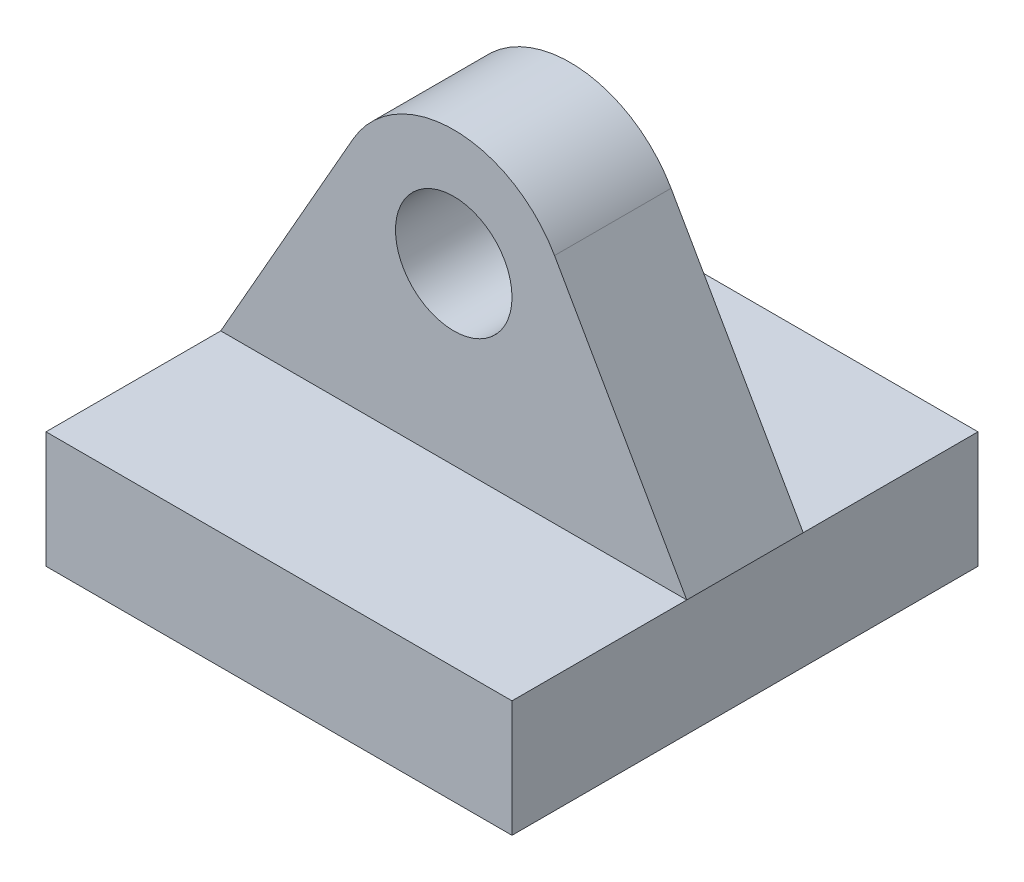
SolidWorks part; units mm, degrees
ref_plane "Front Plane" through (0, 0, 0) normal (0, 0, 1) x (1, 0, 0)
ref_plane "Top Plane" through (0, 0, 0) normal (0, 1, 0) x (1, 0, 0)
ref_plane "Right Plane" through (0, 0, 0) normal (1, 0, 0) x (0, 0, -1)
sketch "Sketch1" plane through (0, 0, 0) normal (0, 0, 1) x (1, 0, 0)
  line L1 (-12.7, -3.175) -> (12.7, -3.175)
  line L2 (-12.7, -3.175) -> (-12.7, 3.175)
  line L3 (-12.7, 3.175) -> (12.7, 3.175)
  line L4 (12.7, -3.175) -> (12.7, 3.175)
  line L5 (-12.7, -3.175) -> (12.7, 3.175) construction
  line L6 (-12.7, 3.175) -> (12.7, -3.175) construction
  point P0 (0, 0)
  dimension "D1" = 25.4
  dimension "D2" = 6.35
extrude "Boss-Extrude1" add sketch "Sketch1" along normal mid plane 25.4
sketch "Sketch2" plane through (0, 0, 0) normal (0, 0, 1) x (1, 0, 0)
  line L0 (-12.7, 3.175) -> (-5.4937, 15.8287)
  line L1 (0, 0) -> (0, 12.7) construction
  line L2 (12.7, 3.175) -> (5.4937, 15.8287)
  line L4 (-12.7, 3.175) -> (12.7, 3.175)
  arc A0 (5.4937, 15.8287) -> (-5.4937, 15.8287) centre (0, 12.7) ccw
  circle A1 centre (0, 12.7) radius 3.175
  dimension "D2" = 12.6442
  dimension "D3" = 6.35
  dimension "D1" = 12.7
extrude "Boss-Extrude2" add sketch "Sketch2" along normal mid plane 6.35
